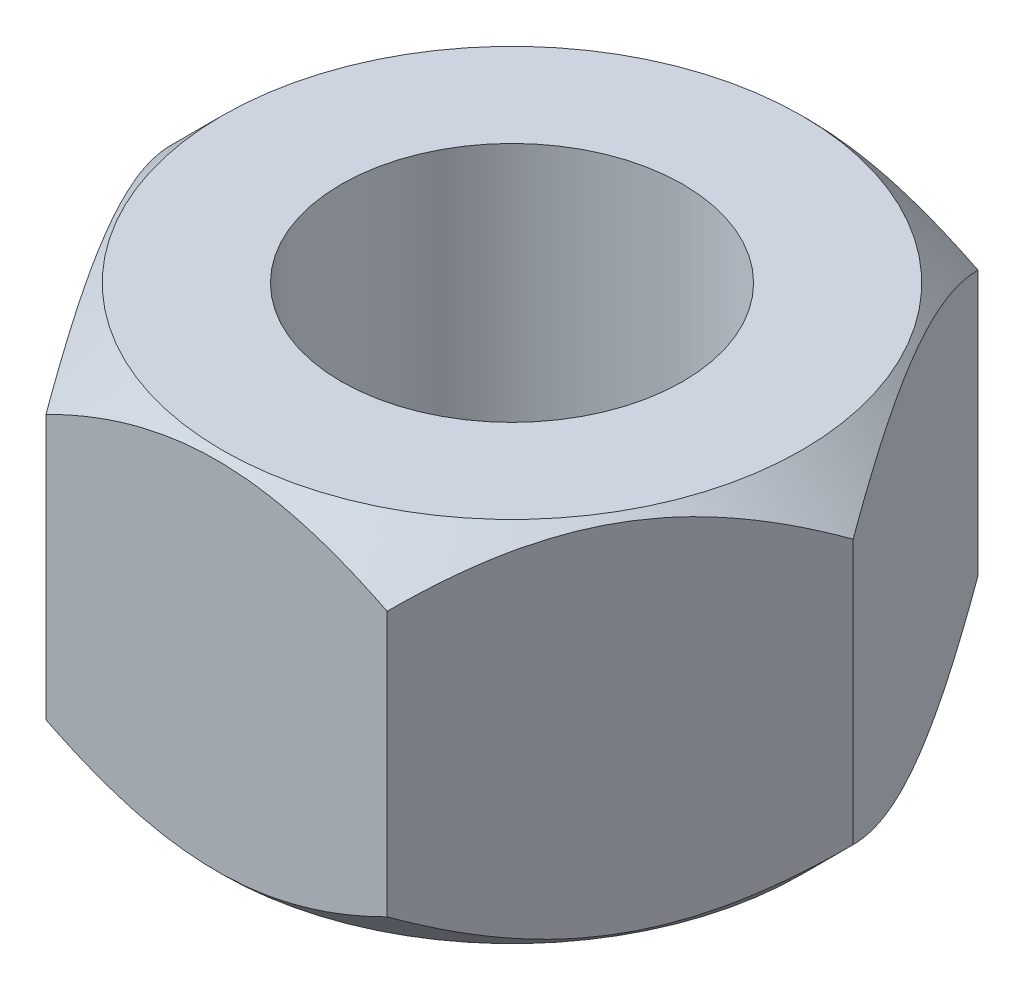
SolidWorks part; units mm, degrees
material "ASTM A36 Acero"
ref_plane "Alzado" through (0, 0, 0) normal (0, 0, 1) x (1, 0, 0)
ref_plane "Planta" through (0, 0, 0) normal (0, 1, 0) x (1, 0, 0)
ref_plane "Vista lateral" through (0, 0, 0) normal (1, 0, 0) x (0, 0, -1)
sketch "Croquis1" plane through (0, 0, 0) normal (0, 1, 0) x (1, 0, 0)
  line L1 (13.2791, 0) -> (6.6395, 11.5)
  line L2 (6.6395, 11.5) -> (-6.6395, 11.5)
  line L3 (-6.6395, 11.5) -> (-13.2791, 0)
  line L4 (-13.2791, 0) -> (-6.6395, -11.5)
  line L5 (-6.6395, -11.5) -> (6.6395, -11.5)
  line L6 (6.6395, -11.5) -> (13.2791, 0)
  circle A0 centre (0, 0) radius 6.65
  circle A1 centre (0, 0) radius 11.5 construction
  dimension "D1" = 13.3
  dimension "D2" = 23
extrude "Saliente-Extruir1" add sketch "Croquis1" along normal mid plane 14.3
sketch "Croquis2" plane through (0, 0, 0) normal (0, 0, 1) x (1, 0, 0)
  line L0 (-11.2791, 7.15) -> (-13.2791, 5.15)
  line L1 (-13.2791, 7.15) -> (-13.2791, -7.15) construction
  line L2 (-13.2791, 5.15) -> (-13.2791, 7.15)
  line L3 (-13.2791, 7.15) -> (-11.2791, 7.15)
  line L4 (-13.2791, 7.15) -> (-6.6395, 7.15) construction
  line L5 (0, 7.15) -> (0, 7.414) construction
  line L6 (-6.6395, 7.15) -> (6.6395, 7.15) construction
  dimension "D1" = 2
revolve "Cortar-Revolución1" cut sketch "Croquis2" angle 360 about L5
mirror "Simetría1" about plane through (0, 0, 0) normal (0, 1, 0) of "Cortar-Revolución1"
